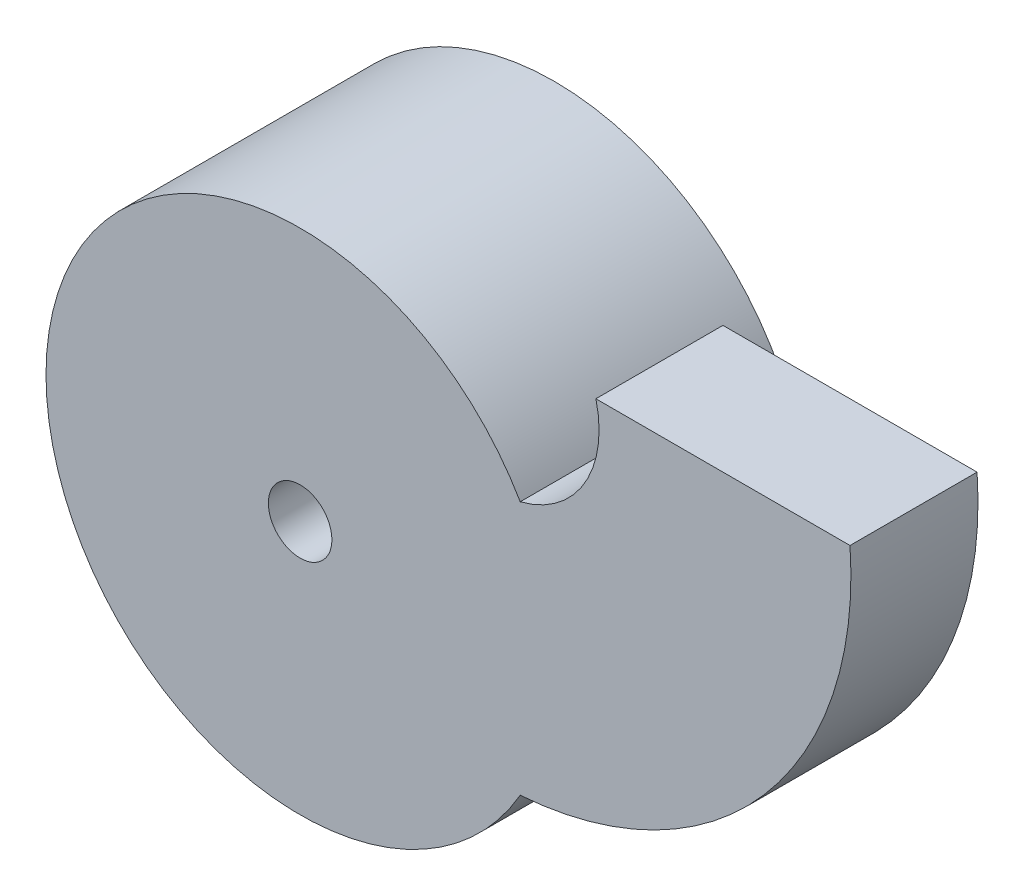
SolidWorks part; units mm, degrees
ref_plane "Front Plane" through (0, 0, 0) normal (0, 0, 1) x (1, 0, 0)
ref_plane "Top Plane" through (0, 0, 0) normal (0, 1, 0) x (1, 0, 0)
ref_plane "Right Plane" through (0, 0, 0) normal (1, 0, 0) x (0, 0, -1)
sketch "Sketch1" plane through (0, 0, 0) normal (0, 0, 1) x (1, 0, 0)
  line L0 (0, 0) -> (40, 0)
  line L1 (-46.5491, -20) -> (-46.5491, -60) construction
  line L2 (-46.5491, -40) -> (-20, -40) construction
  line L3 (0, 0) -> (-100.2458, 0) construction
  arc A0 (-11.9081, -20) -> (-11.9081, -60) centre (-46.5491, -40) ccw
  arc A1 (20, 0) -> (-20, -40) centre (-15.9541, -4.0459) cw construction
  arc A2 (0, 0) -> (-11.9081, -20) centre (-15.9541, -4.0459) cw
  arc A3 (40, 0) -> (-11.9081, -60) centre (-15.9541, -4.0459) cw
  circle A4 centre (-46.5491, -40) radius 5
  point P5 (20, 0)
  point P11 (-46.5491, -40)
  dimension "D1" = 80
  dimension "D4" = 10
  dimension "D2" = 40
  dimension "D3" = 40
extrude "Boss-Extrude1" add sketch "Sketch1" along normal blind 20
sketch "Sketch2" plane through (0, 0, 0) normal (0, 0, -1) x (-1, 0, 0)
  circle A0 centre (46.5491, -40) radius 40
  circle A1 centre (46.5491, -40) radius 5
  dimension "D1" = 80
  dimension "D2" = 10
extrude "Boss-Extrude2" add sketch "Sketch2" along normal blind 20 contours A1 | A0
